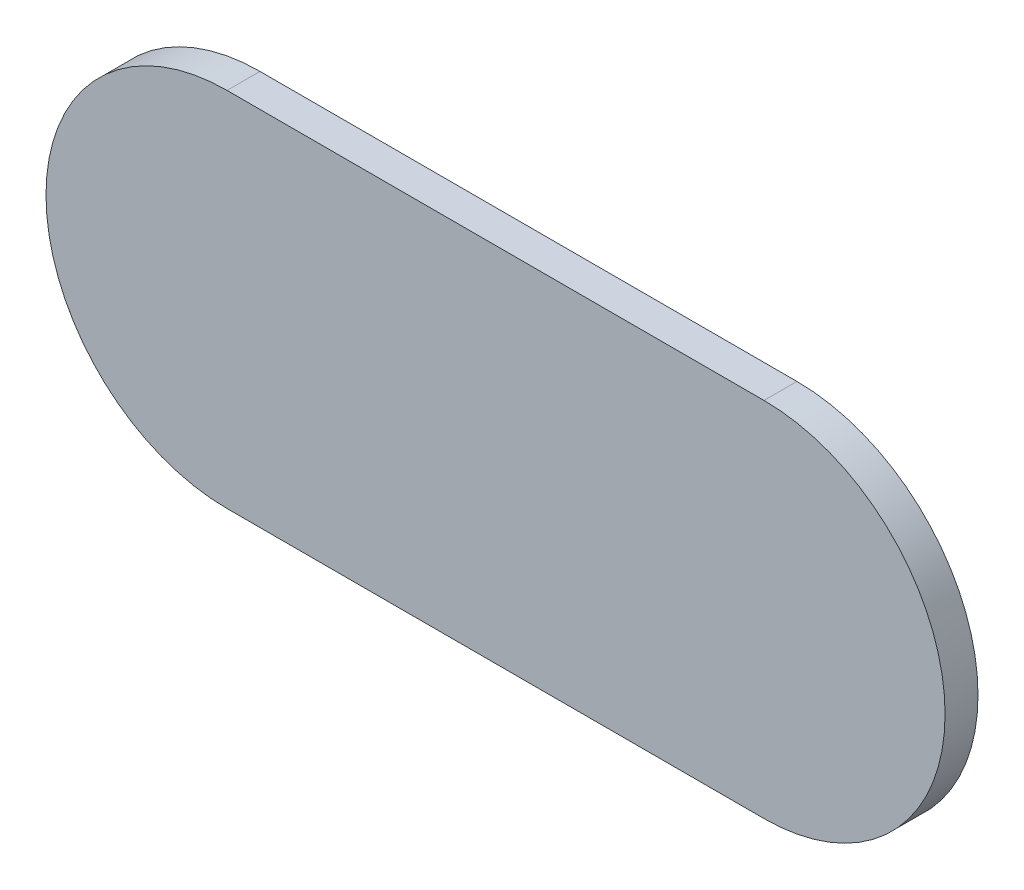
SolidWorks part; units mm, degrees
ref_plane "Front Plane" through (0, 0, 0) normal (0, 0, 1) x (1, 0, 0)
ref_plane "Top Plane" through (0, 0, 0) normal (0, 1, 0) x (1, 0, 0)
ref_plane "Right Plane" through (0, 0, 0) normal (1, 0, 0) x (0, 0, -1)
sketch "Sketch1" plane through (0, 0, 0) normal (0, 0, 1) x (1, 0, 0)
  line L0 (-46.5861, -5.0276) -> (-38.4308, -5.0276) construction
  line L1 (-46.5861, -2.2776) -> (-38.4308, -2.2776)
  line L2 (-46.5861, -7.7776) -> (-38.4308, -7.7776)
  arc A0 (-46.5861, -2.2776) -> (-46.5861, -7.7776) centre (-46.5861, -5.0276) ccw
  arc A1 (-38.4308, -7.7776) -> (-38.4308, -2.2776) centre (-38.4308, -5.0276) ccw
  point P2 (-42.5084, -5.0276)
  dimension "D1" = 2.75
extrude "Boss-Extrude1" add sketch "Sketch1" along normal blind 0.5
